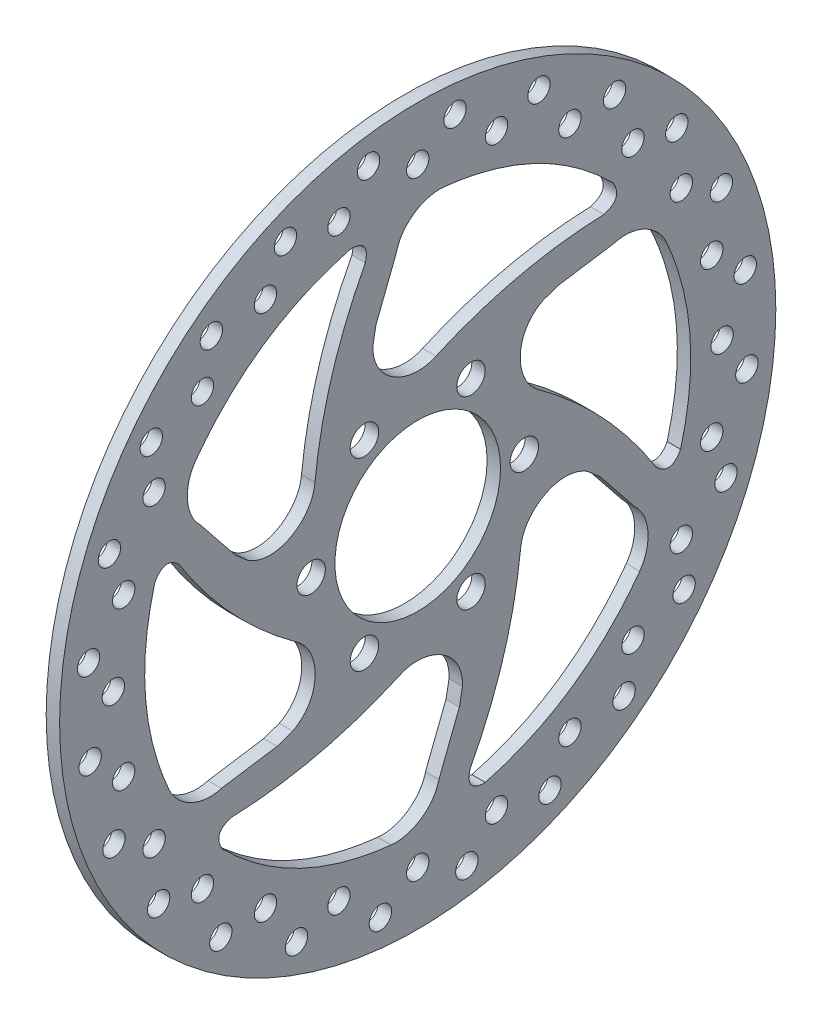
SolidWorks part; units mm, degrees
ref_plane "Front Plane" through (0, 0, 0) normal (0, 0, 1) x (1, 0, 0)
ref_plane "Top Plane" through (0, 0, 0) normal (0, 1, 0) x (1, 0, 0)
ref_plane "Right Plane" through (0, 0, 0) normal (1, 0, 0) x (0, 0, -1)
sketch "Sketch1" plane through (0, 0, 0) normal (1, 0, 0) x (0, 0, -1)
  line L6 (-9.316, 41.6349) -> (-4.7427, 53.3559)
  line L7 (31.3989, 28.8853) -> (43.8362, 30.7853)
  line L8 (40.7149, -12.7495) -> (48.5789, -22.5706)
  line L9 (9.316, -41.6349) -> (4.7427, -53.3559)
  line L10 (-31.3989, -28.8853) -> (-43.8362, -30.7853)
  line L11 (-40.7149, 12.7495) -> (-48.5789, 22.5706)
  line L12 (0, 0) -> (0, -18.5) construction
  circle A49 centre (0, 0) radius 80
  circle A50 centre (0, 68) radius 2.5
  circle A51 centre (8.3322, 73.5294) radius 2.5
  circle A52 centre (17.5997, 65.683) radius 2.5
  circle A53 centre (27.0791, 68.8674) radius 2.5
  circle A54 centre (34, 58.8897) radius 2.5
  circle A55 centre (43.9806, 59.5122) radius 2.5
  circle A56 centre (48.0833, 48.0833) radius 2.5
  circle A57 centre (57.8849, 46.1014) radius 2.5
  circle A58 centre (58.8897, 34) radius 2.5
  circle A59 centre (67.8444, 29.5488) radius 2.5
  circle A60 centre (65.683, 17.5997) radius 2.5
  circle A61 centre (73.1805, 10.9825) radius 2.5
  circle A62 centre (68, 0) radius 2.5
  circle A63 centre (73.5294, -8.3322) radius 2.5
  circle A64 centre (65.683, -17.5997) radius 2.5
  circle A65 centre (68.8674, -27.0791) radius 2.5
  circle A66 centre (58.8897, -34) radius 2.5
  circle A67 centre (59.5122, -43.9806) radius 2.5
  circle A68 centre (48.0833, -48.0833) radius 2.5
  circle A69 centre (46.1014, -57.8849) radius 2.5
  circle A70 centre (34, -58.8897) radius 2.5
  circle A71 centre (29.5488, -67.8444) radius 2.5
  circle A72 centre (17.5997, -65.683) radius 2.5
  circle A73 centre (10.9825, -73.1805) radius 2.5
  circle A74 centre (0, -68) radius 2.5
  circle A75 centre (-8.3322, -73.5294) radius 2.5
  circle A76 centre (-17.5997, -65.683) radius 2.5
  circle A77 centre (-27.0791, -68.8674) radius 2.5
  circle A78 centre (-34, -58.8897) radius 2.5
  circle A79 centre (-43.9806, -59.5122) radius 2.5
  circle A80 centre (-48.0833, -48.0833) radius 2.5
  circle A81 centre (-57.8849, -46.1014) radius 2.5
  circle A82 centre (-58.8897, -34) radius 2.5
  circle A83 centre (-67.8444, -29.5488) radius 2.5
  circle A84 centre (-65.683, -17.5997) radius 2.5
  circle A85 centre (-73.1805, -10.9825) radius 2.5
  circle A86 centre (-68, 0) radius 2.5
  circle A87 centre (-73.5294, 8.3322) radius 2.5
  circle A88 centre (-65.683, 17.5997) radius 2.5
  circle A89 centre (-68.8674, 27.0791) radius 2.5
  circle A90 centre (-58.8897, 34) radius 2.5
  circle A91 centre (-59.5122, 43.9806) radius 2.5
  circle A92 centre (-48.0833, 48.0833) radius 2.5
  circle A93 centre (-46.1014, 57.8849) radius 2.5
  circle A94 centre (-34, 58.8897) radius 2.5
  circle A95 centre (-29.5488, 67.8444) radius 2.5
  circle A96 centre (-17.5997, 65.683) radius 2.5
  circle A97 centre (-10.9825, 73.1805) radius 2.5
  circle A98 centre (0, 0) radius 18.5
  circle A99 centre (-11.9063, 20.6222) radius 3.175
  circle A100 centre (11.9063, 20.6222) radius 3.175
  circle A101 centre (23.8125, 0) radius 3.175
  circle A102 centre (11.9063, -20.6222) radius 3.175
  circle A103 centre (-11.9063, -20.6222) radius 3.175
  circle A104 centre (-23.8125, 0) radius 3.175
  spline S0 degree 2 poles (5.9532, 60.7088) (27.9941, 58.3228) (43.6425, 42.6185) knots 0 0 0 1 1 1
  spline S1 degree 2 poles (4.0813, 28.8708) (21.9975, 36.8421) (41.5951, 37.5241) knots 0 0 0 1 1 1
  spline S2 degree 1 poles (-10, 38) (-9.316, 41.6349) knots 0 0 1 1
  spline S3 degree 3 poles (-4.7427, 53.3559) (-3.6172, 58.1411) (1.3644, 61.1789) (5.9532, 60.7088) knots 0 0 0 0 1 1 1 1
  spline S4 degree 3 poles (4.0813, 28.8708) (-1.8873, 26.0232) (-10.3042, 30.435) (-10, 38) knots 0 0 0 0 1 1 1 1
  spline S5 degree 2 poles (41.5951, 37.5241) (45.9407, 38.7363) (43.6425, 42.6185) knots 0 0 0 1 1 1
  spline S6 degree 2 poles (53.2944, -17.2603) (56.5169, -20.4176) (58.7299, -16.4862) knots 0 0 0 1 1 1
  spline S7 degree 2 poles (55.552, 25.1988) (64.506, 4.9178) (58.7299, -16.4862) knots 0 0 0 1 1 1
  spline S8 degree 3 poles (43.8362, 30.7853) (48.5431, 32.2031) (53.6647, 29.4078) (55.552, 25.1988) knots 0 0 0 0 1 1 1 1
  spline S9 degree 1 poles (27.909, 27.6603) (31.3989, 28.8853) knots 0 0 1 1
  spline S10 degree 3 poles (27.0435, 10.9008) (21.5931, 14.646) (21.2054, 24.1412) (27.909, 27.6603) knots 0 0 0 0 1 1 1 1
  spline S11 degree 2 poles (27.0435, 10.9008) (42.905, -0.6293) (53.2944, -17.2603) knots 0 0 0 1 1 1
  spline S12 degree 2 poles (11.6993, -54.7845) (10.5763, -59.1539) (15.0875, -59.1047) knots 0 0 0 1 1 1
  spline S13 degree 2 poles (49.5988, -35.51) (36.5119, -53.405) (15.0875, -59.1047) knots 0 0 0 1 1 1
  spline S14 degree 3 poles (48.5789, -22.5706) (52.1602, -25.938) (52.3003, -31.7711) (49.5988, -35.51) knots 0 0 0 0 1 1 1 1
  spline S15 degree 1 poles (37.909, -10.3397) (40.7149, -12.7495) knots 0 0 1 1
  spline S16 degree 3 poles (22.9622, -17.9699) (23.4804, -11.3771) (31.5096, -6.2938) (37.909, -10.3397) knots 0 0 0 0 1 1 1 1
  spline S17 degree 2 poles (22.9622, -17.9699) (20.9075, -37.4715) (11.6993, -54.7845) knots 0 0 0 1 1 1
  spline S18 degree 2 poles (-41.5951, -37.5241) (-45.9407, -38.7363) (-43.6425, -42.6185) knots 0 0 0 1 1 1
  spline S19 degree 2 poles (-5.9532, -60.7088) (-27.9941, -58.3228) (-43.6425, -42.6185) knots 0 0 0 1 1 1
  spline S20 degree 3 poles (4.7427, -53.3559) (3.6172, -58.1411) (-1.3644, -61.1789) (-5.9532, -60.7088) knots 0 0 0 0 1 1 1 1
  spline S21 degree 1 poles (10, -38) (9.316, -41.6349) knots 0 0 1 1
  spline S22 degree 3 poles (-4.0813, -28.8708) (1.8873, -26.0232) (10.3042, -30.435) (10, -38) knots 0 0 0 0 1 1 1 1
  spline S23 degree 2 poles (-4.0813, -28.8708) (-21.9975, -36.8421) (-41.5951, -37.5241) knots 0 0 0 1 1 1
  spline S24 degree 2 poles (-53.2944, 17.2603) (-56.5169, 20.4176) (-58.7299, 16.4862) knots 0 0 0 1 1 1
  spline S25 degree 2 poles (-55.552, -25.1988) (-64.506, -4.9178) (-58.7299, 16.4862) knots 0 0 0 1 1 1
  spline S26 degree 3 poles (-43.8362, -30.7853) (-48.5431, -32.2031) (-53.6647, -29.4078) (-55.552, -25.1988) knots 0 0 0 0 1 1 1 1
  spline S27 degree 1 poles (-27.909, -27.6603) (-31.3989, -28.8853) knots 0 0 1 1
  spline S28 degree 3 poles (-27.0435, -10.9008) (-21.5931, -14.646) (-21.2054, -24.1412) (-27.909, -27.6603) knots 0 0 0 0 1 1 1 1
  spline S29 degree 2 poles (-27.0435, -10.9008) (-42.905, 0.6293) (-53.2944, 17.2603) knots 0 0 0 1 1 1
  spline S30 degree 2 poles (-11.6993, 54.7845) (-10.5763, 59.1539) (-15.0875, 59.1047) knots 0 0 0 1 1 1
  spline S31 degree 2 poles (-49.5988, 35.51) (-36.5119, 53.405) (-15.0875, 59.1047) knots 0 0 0 1 1 1
  spline S32 degree 3 poles (-48.5789, 22.5706) (-52.1602, 25.938) (-52.3003, 31.7711) (-49.5988, 35.51) knots 0 0 0 0 1 1 1 1
  spline S33 degree 1 poles (-37.909, 10.3397) (-40.7149, 12.7495) knots 0 0 1 1
  spline S34 degree 3 poles (-22.9622, 17.9699) (-23.4804, 11.3771) (-31.5096, 6.2938) (-37.909, 10.3397) knots 0 0 0 0 1 1 1 1
  spline S35 degree 2 poles (-22.9622, 17.9699) (-20.9075, 37.4715) (-11.6993, 54.7845) knots 0 0 0 1 1 1
extrude "Boss-Extrude1" add sketch "Sketch1" along normal blind 3
